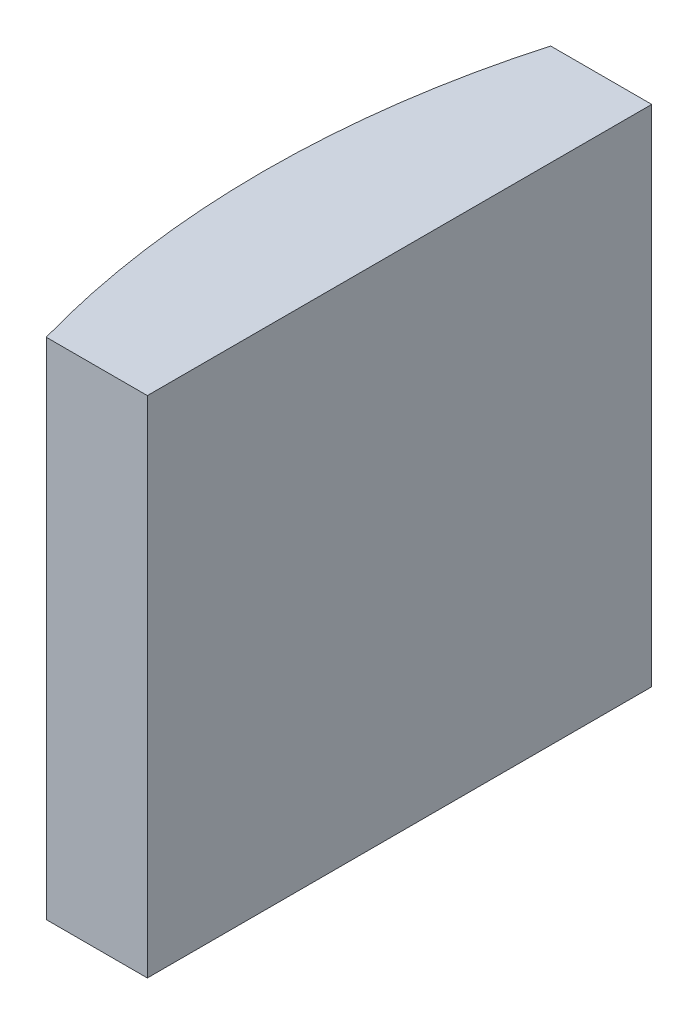
SolidWorks part; units mm, degrees
ref_plane "前视基准面" through (0, 0, 0) normal (0, 0, 1) x (1, 0, 0)
ref_plane "上视基准面" through (0, 0, 0) normal (0, 1, 0) x (1, 0, 0)
ref_plane "右视基准面" through (0, 0, 0) normal (1, 0, 0) x (0, 0, -1)
sketch "草图1" plane through (0, 0, 0) normal (0, 1, 0) x (1, 0, 0)
  line L0 (-23.3839, 0) -> (10.8051, 0) construction
  line L1 (-13.2693, 5) -> (-11.2648, 5)
  line L2 (-13.2693, -5) -> (-11.2648, -5)
  line L3 (-11.2648, 5) -> (-11.2648, -5)
  arc A0 (-13.2693, 5) -> (-13.2693, -5) centre (4.3552, 0) ccw
  point P2 (-13.9648, 0)
  point P4 (-11.2648, 0)
  point P8 (-23.3839, 0)
  dimension "D2" = 5
  dimension "D3" = 18.32
  dimension "D4" = 2.7
  dimension "D1" = 5
extrude "凸台-拉伸1" add sketch "草图1" along normal blind 10
